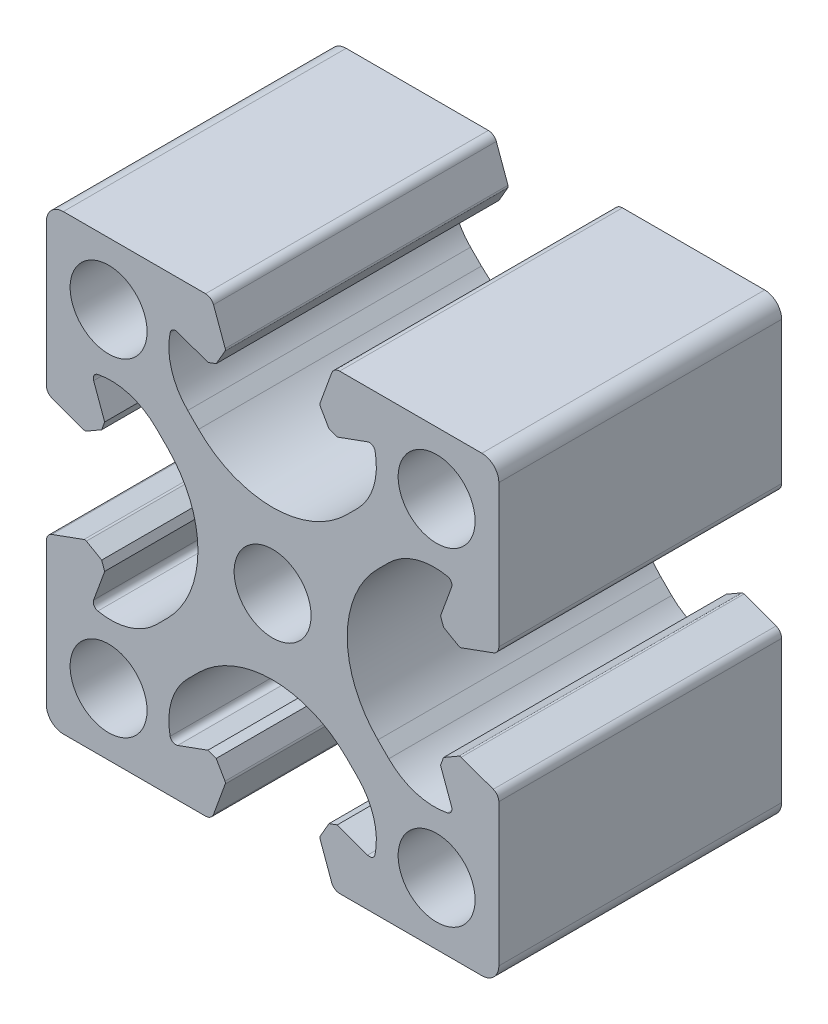
SolidWorks part; units mm, degrees
material "6005-T5"
ref_plane "Front" through (0, 0, 0) normal (0, 0, 1) x (1, 0, 0)
ref_plane "Top" through (0, 0, 0) normal (0, 1, 0) x (1, 0, 0)
ref_plane "Right" through (0, 0, 0) normal (1, 0, 0) x (0, 0, -1)
sketch "Sk Main Extrusion" plane through (0, 0, 0) normal (0, 0, 1) x (1, 0, 0)
  line L60 (4.1901, -16.6712) -> (5.2221, -19.5065)
  line L61 (5.9268, -20) -> (18.5, -20)
  line L62 (20, -18.5) -> (20, -5.9268)
  line L63 (19.5065, -5.2221) -> (16.6712, -4.1901)
  line L64 (16.4607, -4.2085) -> (15.1113, -4.9876)
  line L65 (15.1113, -4.9876) -> (14.8453, -5.7185)
  line L66 (14.8453, -5.7185) -> (15.8198, -8.3962)
  line L67 (10.2727, -7.5042) -> (9.3093, -6.5407)
  line L68 (9.3093, 6.5407) -> (10.2727, 7.5042)
  line L69 (15.8198, 8.3962) -> (14.8453, 5.7185)
  line L70 (14.8453, 5.7185) -> (15.1113, 4.9876)
  line L71 (15.1113, 4.9876) -> (16.4607, 4.2085)
  line L72 (16.6712, 4.1901) -> (19.5065, 5.2221)
  line L73 (20, 5.9268) -> (20, 18.5)
  line L74 (18.5, 20) -> (5.9268, 20)
  line L75 (5.2221, 19.5065) -> (4.1901, 16.6712)
  line L76 (4.2085, 16.4607) -> (4.9876, 15.1113)
  line L77 (4.9876, 15.1113) -> (5.7185, 14.8453)
  line L78 (5.7185, 14.8453) -> (8.3962, 15.8198)
  line L79 (7.5042, 10.2727) -> (6.5407, 9.3093)
  line L80 (-6.5407, 9.3093) -> (-7.5042, 10.2727)
  line L81 (-8.3962, 15.8198) -> (-5.7185, 14.8453)
  line L82 (-5.7185, 14.8453) -> (-4.9876, 15.1113)
  line L83 (-4.9876, 15.1113) -> (-4.2085, 16.4607)
  line L84 (-4.1901, 16.6712) -> (-5.2221, 19.5065)
  line L85 (-5.9268, 20) -> (-18.5, 20)
  line L86 (-20, 18.5) -> (-20, 5.9268)
  line L87 (-19.5065, 5.2221) -> (-16.6712, 4.1901)
  line L88 (-16.4607, 4.2085) -> (-15.1113, 4.9876)
  line L89 (-15.1113, 4.9876) -> (-14.8453, 5.7185)
  line L90 (-14.8453, 5.7185) -> (-15.8198, 8.3962)
  line L91 (-10.2727, 7.5042) -> (-9.3093, 6.5407)
  line L92 (-9.3093, -6.5407) -> (-10.2727, -7.5042)
  line L93 (-15.8198, -8.3962) -> (-14.8453, -5.7185)
  line L94 (-14.8453, -5.7185) -> (-15.1113, -4.9876)
  line L95 (-15.1113, -4.9876) -> (-16.4607, -4.2085)
  line L96 (-16.6712, -4.1901) -> (-19.5065, -5.2221)
  line L97 (-20, -5.9268) -> (-20, -18.5)
  line L98 (-18.5, -20) -> (-5.9268, -20)
  line L99 (-5.2221, -19.5065) -> (-4.1901, -16.6712)
  line L100 (-4.2085, -16.4607) -> (-4.9876, -15.1113)
  line L101 (-4.9876, -15.1113) -> (-5.7185, -14.8453)
  line L102 (-5.7185, -14.8453) -> (-8.3962, -15.8198)
  line L103 (-7.5042, -10.2727) -> (-6.5407, -9.3093)
  line L104 (6.5407, -9.3093) -> (7.5042, -10.2727)
  line L105 (8.3962, -15.8198) -> (5.7185, -14.8453)
  line L106 (5.7185, -14.8453) -> (4.9876, -15.1113)
  line L107 (4.9876, -15.1113) -> (4.2085, -16.4607)
  circle A52 centre (-14.5, -14.5) radius 3.4
  circle A53 centre (14.5, -14.5) radius 3.4
  circle A54 centre (14.5, 14.5) radius 3.4
  circle A55 centre (-14.5, 14.5) radius 3.4
  circle A56 centre (0, 0) radius 3.4
  arc A57 (5.2221, -19.5065) -> (5.9268, -20) centre (5.9268, -19.25) ccw
  arc A58 (18.5, -20) -> (20, -18.5) centre (18.5, -18.5) ccw
  arc A59 (20, -5.9268) -> (19.5065, -5.2221) centre (19.25, -5.9268) ccw
  arc A60 (16.6712, -4.1901) -> (16.4607, -4.2085) centre (16.5857, -4.425) ccw
  arc A61 (15.4507, -9.057) -> (15.8198, -8.3962) centre (15.35, -8.5672) ccw
  arc A62 (10.2727, -7.5042) -> (15.4507, -9.057) centre (14.3032, -3.4737) ccw
  arc A63 (9.3093, 6.5407) -> (9.3093, -6.5407) centre (15.85, 0) ccw
  arc A64 (15.4507, 9.057) -> (10.2727, 7.5042) centre (14.3032, 3.4737) ccw
  arc A65 (15.8198, 8.3962) -> (15.4507, 9.057) centre (15.35, 8.5672) ccw
  arc A66 (16.4607, 4.2085) -> (16.6712, 4.1901) centre (16.5857, 4.425) ccw
  arc A67 (19.5065, 5.2221) -> (20, 5.9268) centre (19.25, 5.9268) ccw
  arc A68 (20, 18.5) -> (18.5, 20) centre (18.5, 18.5) ccw
  arc A69 (5.9268, 20) -> (5.2221, 19.5065) centre (5.9268, 19.25) ccw
  arc A70 (4.1901, 16.6712) -> (4.2085, 16.4607) centre (4.425, 16.5857) ccw
  arc A71 (9.057, 15.4507) -> (8.3962, 15.8198) centre (8.5672, 15.35) ccw
  arc A72 (7.5042, 10.2727) -> (9.057, 15.4507) centre (3.4737, 14.3032) ccw
  arc A73 (-6.5407, 9.3093) -> (6.5407, 9.3093) centre (0, 15.85) ccw
  arc A74 (-9.057, 15.4507) -> (-7.5042, 10.2727) centre (-3.4737, 14.3032) ccw
  arc A75 (-8.3962, 15.8198) -> (-9.057, 15.4507) centre (-8.5672, 15.35) ccw
  arc A76 (-4.2085, 16.4607) -> (-4.1901, 16.6712) centre (-4.425, 16.5857) ccw
  arc A77 (-5.2221, 19.5065) -> (-5.9268, 20) centre (-5.9268, 19.25) ccw
  arc A78 (-18.5, 20) -> (-20, 18.5) centre (-18.5, 18.5) ccw
  arc A79 (-20, 5.9268) -> (-19.5065, 5.2221) centre (-19.25, 5.9268) ccw
  arc A80 (-16.6712, 4.1901) -> (-16.4607, 4.2085) centre (-16.5857, 4.425) ccw
  arc A81 (-15.4507, 9.057) -> (-15.8198, 8.3962) centre (-15.35, 8.5672) ccw
  arc A82 (-10.2727, 7.5042) -> (-15.4507, 9.057) centre (-14.3032, 3.4737) ccw
  arc A83 (-9.3093, -6.5407) -> (-9.3093, 6.5407) centre (-15.85, 0) ccw
  arc A84 (-15.4507, -9.057) -> (-10.2727, -7.5042) centre (-14.3032, -3.4737) ccw
  arc A85 (-15.8198, -8.3962) -> (-15.4507, -9.057) centre (-15.35, -8.5672) ccw
  arc A86 (-16.4607, -4.2085) -> (-16.6712, -4.1901) centre (-16.5857, -4.425) ccw
  arc A87 (-19.5065, -5.2221) -> (-20, -5.9268) centre (-19.25, -5.9268) ccw
  arc A88 (-20, -18.5) -> (-18.5, -20) centre (-18.5, -18.5) ccw
  arc A89 (-5.9268, -20) -> (-5.2221, -19.5065) centre (-5.9268, -19.25) ccw
  arc A90 (-4.1901, -16.6712) -> (-4.2085, -16.4607) centre (-4.425, -16.5857) ccw
  arc A91 (-9.057, -15.4507) -> (-8.3962, -15.8198) centre (-8.5672, -15.35) ccw
  arc A92 (-7.5042, -10.2727) -> (-9.057, -15.4507) centre (-3.4737, -14.3032) ccw
  arc A93 (6.5407, -9.3093) -> (-6.5407, -9.3093) centre (0, -15.85) ccw
  arc A94 (9.057, -15.4507) -> (7.5042, -10.2727) centre (3.4737, -14.3032) ccw
  arc A95 (8.3962, -15.8198) -> (9.057, -15.4507) centre (8.5672, -15.35) ccw
  arc A96 (4.2085, -16.4607) -> (4.1901, -16.6712) centre (4.425, -16.5857) ccw
  point P82 (0, 0)
extrude "Main Extrusion" add sketch "Sk Main Extrusion" against normal blind 25
sketch "Threaded Insert Mate Sketch" plane through (0, 0, 0) normal (0, 0, 1) x (1, 0, 0)
  circle A0 centre (0, 12.7) radius 5.6515
  circle A1 centre (12.7, 0) radius 5.6515
  circle A2 centre (0, -12.7) radius 5.6515
  circle A3 centre (-12.7, 0) radius 5.6515
  point P12 (0, 0)
  dimension "D2" = 11.303
  dimension "D1" = 12.7
  dimension "D3" = 4
equation "\"Weight kg\"= round ( \"SW-Mass\" , 2 )"
equation "\"Weight lbs\"= round ( \"SW-Mass\" * 2.2046 , 2 )"
equation "\"Length mm\"= round ( \"Length@Main Extrusion\" , 2 )"
equation "\"Length in\"= round ( \"Length@Main Extrusion\" / 25.4 , 3 )"
